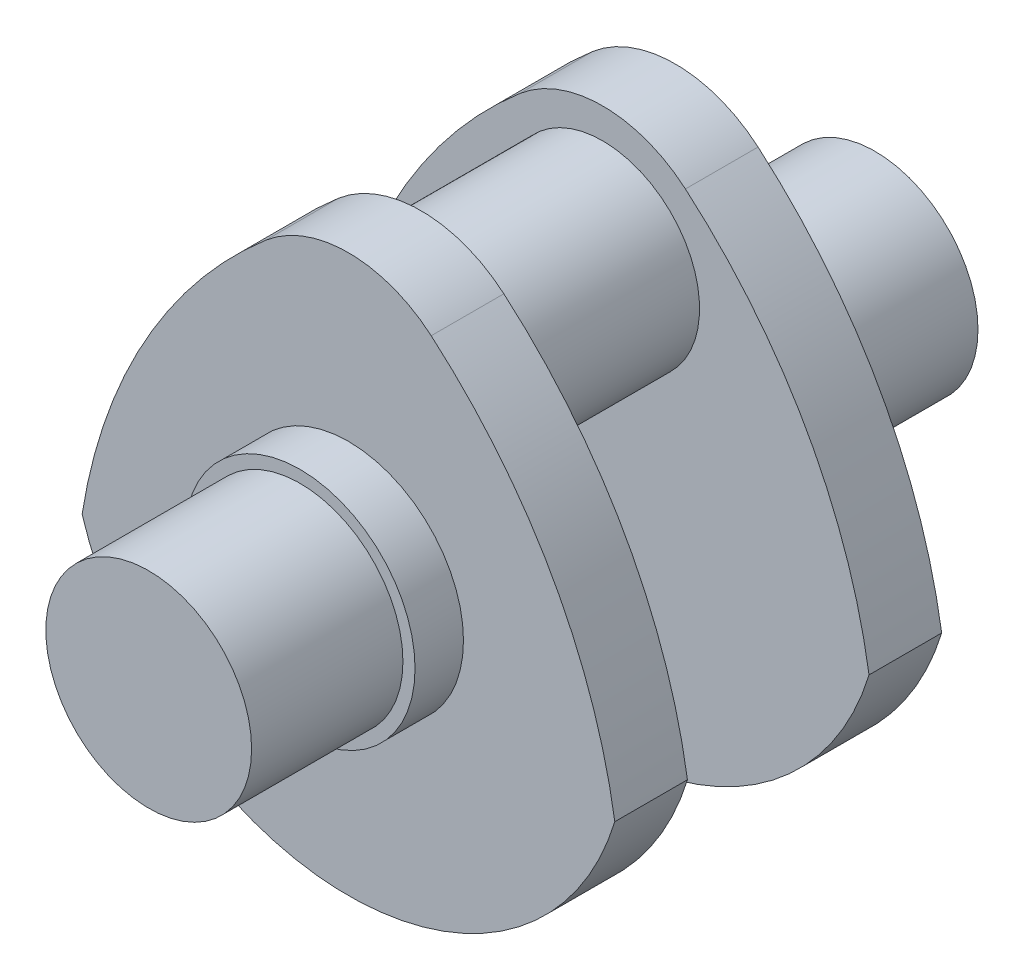
SolidWorks part; units mm, degrees
ref_plane "Front Plane" through (0, 0, 0) normal (0, 0, 1) x (1, 0, 0)
ref_plane "Top Plane" through (0, 0, 0) normal (0, 1, 0) x (1, 0, 0)
ref_plane "Right Plane" through (0, 0, 0) normal (1, 0, 0) x (0, 0, -1)
sketch "Sketch1" plane through (0, 0, 0) normal (0, 0, 1) x (1, 0, 0)
  circle A0 centre (0, 0) radius 170
  dimension "D2" = 340
extrude "Boss-Extrude1" add sketch "Sketch1" along normal blind 250
sketch "Sketch2" plane through (0, 0, 0) normal (0, 0, -1) x (-1, 0, 0)
  circle A0 centre (0, 0) radius 190
  dimension "D1" = 380
extrude "Boss-Extrude2" add sketch "Sketch2" along normal blind 80
sketch "Sketch3" plane through (0, 0, -80) normal (0, 0, -1) x (-1, 0, 0)
  arc A0 (-440, -134.1641) -> (440, -134.1641) centre (0, 0) ccw
  arc A1 (136.6809, 409.4312) -> (-136.6809, 409.4312) centre (0, 250) ccw
  arc A2 (136.6809, 409.4312) -> (440, -134.1641) centre (-449.0945, -273.8455) cw
  arc A3 (-136.6809, 409.4312) -> (-440, -134.1641) centre (449.0945, -273.8455) ccw
  point P10 (0, 0)
  dimension "D2" = 460
  dimension "D4" = 420
  dimension "D5" = 900
  dimension "D6" = 900
  dimension "D1" = 880
  dimension "D3" = 250
extrude "Boss-Extrude3" add sketch "Sketch3" along normal blind 120
sketch "Sketch4" plane through (0, 0, -200) normal (0, 0, -1) x (-1, 0, 0)
  circle A0 centre (0, 250) radius 160
  dimension "D1" = 320
  dimension "D2" = 250
extrude "Boss-Extrude4" add sketch "Sketch4" along normal blind 150
mirror "Mirror1" about plane through (0, 250, -350) normal (0, 0, -1) of bodies 104
